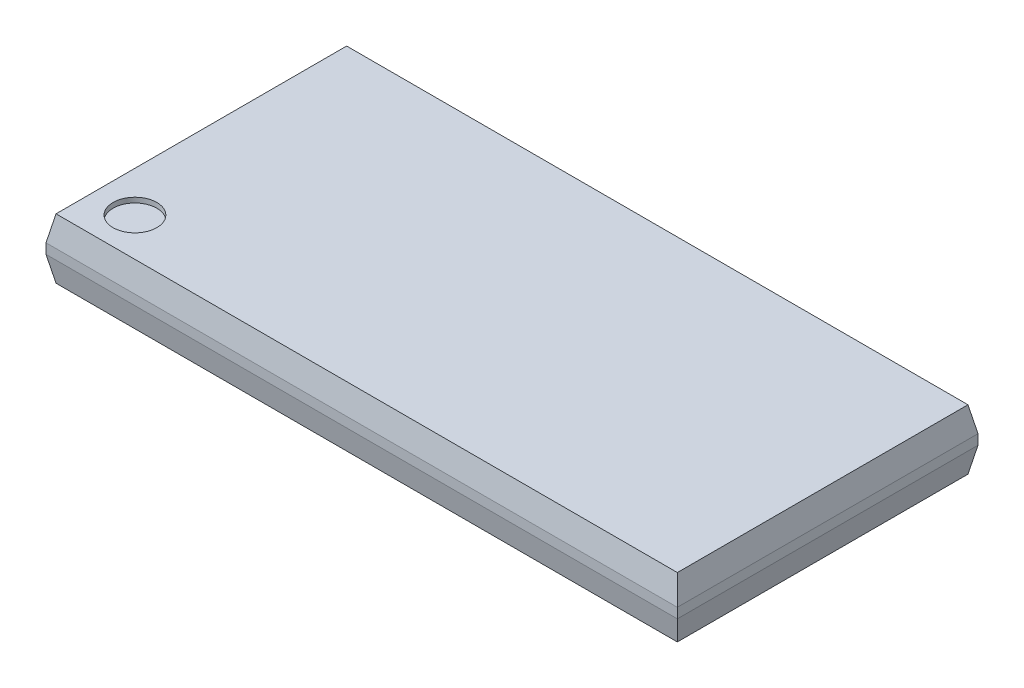
SolidWorks part; units mm, degrees
ref_plane "Plan de face" through (0, 0, 0) normal (0, 0, 1) x (1, 0, 0)
ref_plane "Plan de dessus" through (0, 0, 0) normal (0, 1, 0) x (1, 0, 0)
ref_plane "Plan de droite" through (0, 0, 0) normal (1, 0, 0) x (0, 0, -1)
sketch "Esquisse1" plane through (0, 0, 0) normal (0, 1, 0) x (1, 0, 0)
  line L1 (0, 0) -> (12.6, 0)
  line L2 (0, 0) -> (0, 6)
  line L3 (0, 6) -> (12.6, 6)
  line L4 (12.6, 0) -> (12.6, 6)
extrude "Boss.-Extru.1" add sketch "Esquisse1" along normal blind 1.2
chamfer "Chanfrein1" distance 0.5 distance2 0.1 1 edges at (6.3, 1.2, 0)
chamfer "Chanfrein2" distance 0.1 distance2 0.5 1 edges at (6.3, 0, 0)
chamfer "Chanfrein3" distance 0.5 distance2 0.1 1 edges at (6.3, 1.2, -6)
chamfer "Chanfrein4" distance 0.1 distance2 0.5 1 edges at (6.3, 0, -6)
chamfer "Chanfrein5" distance 0.5 distance2 0.1 1 edges at (0, 1.2, -3)
chamfer "Chanfrein6" distance 0.1 distance2 0.5 1 edges at (0, 0, -3)
chamfer "Chanfrein7" distance 0.5 distance2 0.1 1 edges at (12.6, 1.2, -3)
chamfer "Chanfrein8" distance 0.1 distance2 0.5 1 edges at (12.6, 0, -3)
sketch "Esquisse2" plane through (0, 1.2, 0) normal (0, 1, 0) x (-1, 0, 0)
  circle A0 centre (-0.9088, -0.8662) radius 0.4362
extrude "Enlèv. mat.-Extru.1" cut sketch "Esquisse2" against normal blind 0.1
